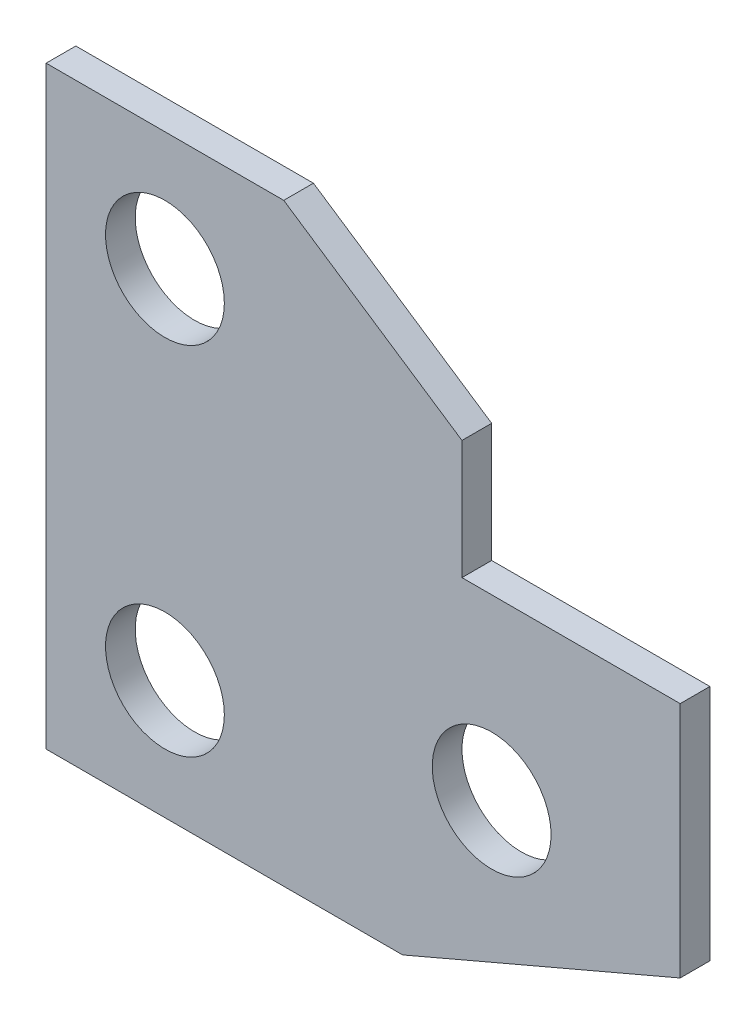
SolidWorks part; units mm, degrees
ref_plane "Front Plane" through (0, 0, 0) normal (0, 0, 1) x (1, 0, 0)
ref_plane "Top Plane" through (0, 0, 0) normal (0, 1, 0) x (1, 0, 0)
ref_plane "Right Plane" through (0, 0, 0) normal (1, 0, 0) x (0, 0, -1)
sketch "Sketch2" plane through (0, 0, 0) normal (0, 0, 1) x (1, 0, 0)
  line L0 (-283.4493, 580.4905) -> (684.4574, 580.4905) construction
  line L1 (-146.8472, 106.2354) -> (-106.8472, 106.2354)
  line L2 (-106.8472, 106.2354) -> (-76.8472, 86.2354)
  line L3 (-76.8472, 86.2354) -> (-76.8472, 66.2354)
  line L4 (-76.8472, 66.2354) -> (-40.1141, 66.2354)
  line L5 (-40.1141, 66.2354) -> (-40.1141, 26.2354)
  line L6 (-40.1141, 26.2354) -> (-86.8472, 6.2354)
  line L7 (-86.8472, 6.2354) -> (-146.8472, 6.2354)
  line L8 (-146.8472, 6.2354) -> (-146.8472, 106.2354)
  line L9 (-86.8472, 6.2354) -> (-40.1141, 6.2354) construction
  line L10 (-106.8472, 106.2354) -> (-76.8472, 106.2354) construction
  line L11 (-76.8472, 86.2354) -> (-76.8472, 106.2354) construction
  line L12 (-126.8472, 86.2354) -> (-126.8472, 26.2354) construction
  circle A0 centre (-126.8472, 86.2354) radius 10
  circle A1 centre (-126.8472, 26.2354) radius 10
  circle A2 centre (-71.8472, 36.2354) radius 10
  point P18 (0, 0)
  dimension "D9" = 20
  dimension "D10" = 20
  dimension "D14" = 20
  dimension "D1" = 100
  dimension "D2" = 60
  dimension "D3" = 40
  dimension "D4" = 40
  dimension "D5" = 20
  dimension "D6" = 20
  dimension "D7" = 70
  dimension "D8" = 60
  dimension "D11" = 60
  dimension "D12" = 20
  dimension "D13" = 20
  dimension "D15" = 30
  dimension "D16" = 75
extrude "Boss-Extrude1" add sketch "Sketch2" along normal blind 5
